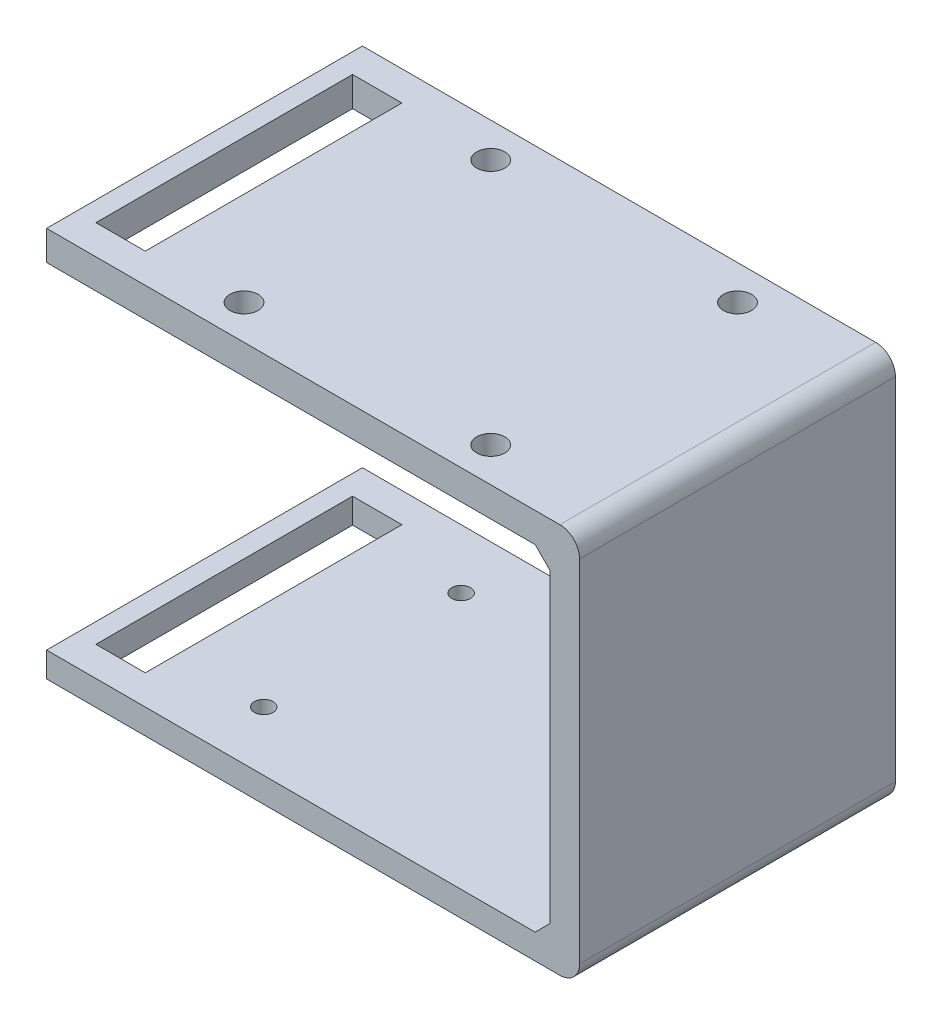
SolidWorks part; units mm, degrees
ref_plane "Front Plane" through (0, 0, 0) normal (0, 0, 1) x (1, 0, 0)
ref_plane "Top Plane" through (0, 0, 0) normal (0, 1, 0) x (1, 0, 0)
ref_plane "Right Plane" through (0, 0, 0) normal (1, 0, 0) x (0, 0, -1)
sketch "Sketch1" plane through (0, 0, 0) normal (0, 1, 0) x (1, 0, 0)
  line L0 (20, 0) -> (-20, 0)
  line L1 (-20, 0) -> (-20, -20)
  line L2 (-20, -10) -> (20, -10) construction
  line L3 (20, 0) -> (20, -20)
  line L4 (20, -20) -> (-20, -20)
  line L5 (26, 6) -> (-26, 6)
  line L6 (-26, 6) -> (-26, -26)
  line L7 (26, -26) -> (-26, -26)
  line L8 (26, 6) -> (26, -26)
  line L10 (26, 6) -> (28, 6)
  line L11 (26, 6) -> (26, -26)
  line L12 (26, -26) -> (28, -26)
  line L13 (28, 6) -> (28, -26)
  line L14 (27, -26) -> (27, 6) construction
  line L15 (26, -10) -> (28, -10) construction
  circle A0 centre (-10, 0) radius 0.95
  circle A1 centre (-10, -20) radius 0.95
  circle A2 centre (20, -10) radius 0.95
  circle A3 centre (20, -10) radius 1.8
  circle A4 centre (-10, 0) radius 1.8
  circle A5 centre (-10, -20) radius 1.8
  point P4 (0, 0)
  point P14 (0, -20)
  point P210 (27, -10)
  dimension "D2" = 1.9
  dimension "D5" = 1.9
  dimension "D1" = 40
  dimension "D3" = 10
  dimension "D4" = 10
  dimension "D8" = 32
  dimension "D9" = 2
  dimension "D6" = 0.85
  dimension "D7" = 0.85
extrude "Boss-Extrude1" add sketch "Sketch1" along normal blind 2.54 contours L8 L5 L6 L7 L4 A5 L1 L0 A4 L3 A3 | L4 A5 L3 A3 L0 A4 L1 | L0 A4 A0 | L0 A4 A0 | A5 L4 A1 | A5 L4 A1 | L3 A3 A2 | L3 A3 A2 | L13 L10 L8 L12
sketch "Sketch3" plane through (0, 2.54, 0) normal (0, 1, 0) x (1, 0, 0)
  line L0 (28, 6) -> (-26, 6) construction
  line L1 (25, 6) -> (28, 6)
  line L2 (25, 6) -> (25, -26)
  line L3 (25, -26) -> (28, -26)
  line L4 (28, 6) -> (28, -26)
  line L5 (26.5, -26) -> (26.5, 6) construction
  line L6 (25, -10) -> (28, -10) construction
  point P268 (26.5, -10)
  dimension "D1" = 3
extrude "Boss-Extrude2" add sketch "Sketch3" along normal blind 37
sketch "Sketch4" plane through (25, 0, 0) normal (-1, 0, 0) x (0, 0, 1)
  line L0 (26, 39.54) -> (26, 2.54) construction
  line L1 (-6, 39.54) -> (26, 39.54)
  line L2 (-6, 39.54) -> (-6, 36.54)
  line L3 (-6, 36.54) -> (26, 36.54)
  line L4 (26, 39.54) -> (26, 36.54)
  line L5 (10, 36.54) -> (10, 39.54) construction
  line L6 (-6, 38.04) -> (26, 38.04) construction
  point P212 (10, 38.04)
  dimension "D1" = 3
extrude "Boss-Extrude3" add sketch "Sketch4" along normal blind 47
fillet "Fillet1" radius 2 2 edges at (28, 0, 10) (28, 39.54, 10)
sketch "Sketch5" plane through (0, 39.54, 0) normal (0, 1, 0) x (1, 0, 0)
  line L0 (-22, -10) -> (28, -10) construction
  line L1 (-22, -26) -> (-22, 6) construction
  line L2 (28, 6) -> (28, -26) construction
  line L3 (3, -10) -> (3, 5) construction
  line L4 (19, -26) -> (19, 6)
  line L5 (19, -26) -> (-13, -26)
  line L6 (19, 6) -> (-13, 6)
  line L7 (-13, -26) -> (-13, 6)
  line L8 (19, -26) -> (-13, 6) construction
  line L9 (19, 6) -> (-13, -26) construction
  line L10 (-12, -25) -> (-12, 5)
  line L11 (18, 5) -> (-12, 5)
  line L12 (18, -25) -> (18, 5)
  line L13 (18, -25) -> (-12, -25)
  circle A0 centre (-9.5, 2.5) radius 1.425
  circle A1 centre (15.5, 2.5) radius 1.425
  circle A2 centre (15.5, -22.5) radius 1.425
  circle A3 centre (-9.5, -22.5) radius 1.425
  dimension "D5" = 2.85
  dimension "D1" = 15
  dimension "D2" = 32
  dimension "D3" = 32
  dimension "D4" = 30
  dimension "D6" = 2.5
extrude "Cut-Extrude1" cut sketch "Sketch5" against normal blind 20 contours A0 | A1 | A2 | A3 | L7 L6 L4 L5
sketch "Sketch6" plane through (0, 2.54, 0) normal (0, 1, 0) x (1, 0, 0)
  line L1 (-26, 6) -> (-22, 6)
  line L2 (-26, 6) -> (-26, -26)
  line L3 (-26, -26) -> (-22, -26)
  line L4 (-22, 6) -> (-22, -26)
  line L5 (-24, -26) -> (-24, 6) construction
  line L6 (-26, -10) -> (-22, -10) construction
  point P108 (-24, -10)
sketch "Sketch8" plane through (-22, 0, 0) normal (-1, 0, 0) x (0, 0, 1)
  line L1 (-6, 39.54) -> (26, 39.54)
  line L2 (-6, 39.54) -> (-6, 36.54)
  line L3 (-6, 36.54) -> (26, 36.54)
  line L4 (26, 39.54) -> (26, 36.54)
  line L5 (10, 36.54) -> (10, 39.54) construction
  line L6 (-6, 38.04) -> (26, 38.04) construction
  point P76 (10, 38.04)
extrude "Boss-Extrude4" add sketch "Sketch8" along normal blind 4
sketch "Sketch7" plane through (0, 39.54, 0) normal (0, 1, 0) x (1, 0, 0)
  line L0 (26, 6) -> (-26, 6) construction
  line L1 (-24, 3) -> (-19, 3)
  line L2 (-24, 3) -> (-24, -23)
  line L3 (-24, -23) -> (-19, -23)
  line L4 (-19, 3) -> (-19, -23)
  line L5 (-26, 6) -> (-26, -26) construction
  point P10 (0, 0)
  dimension "D1" = 5
  dimension "D2" = 26
  dimension "D3" = 3
  dimension "D4" = 2
extrude "Cut-Extrude3" cut sketch "Sketch7" against normal through all both and the other way through all
chamfer "Chamfer1" distance 1.5 angle 45 2 edges at (25, 36.54, 10) (25, 2.54, 10)
